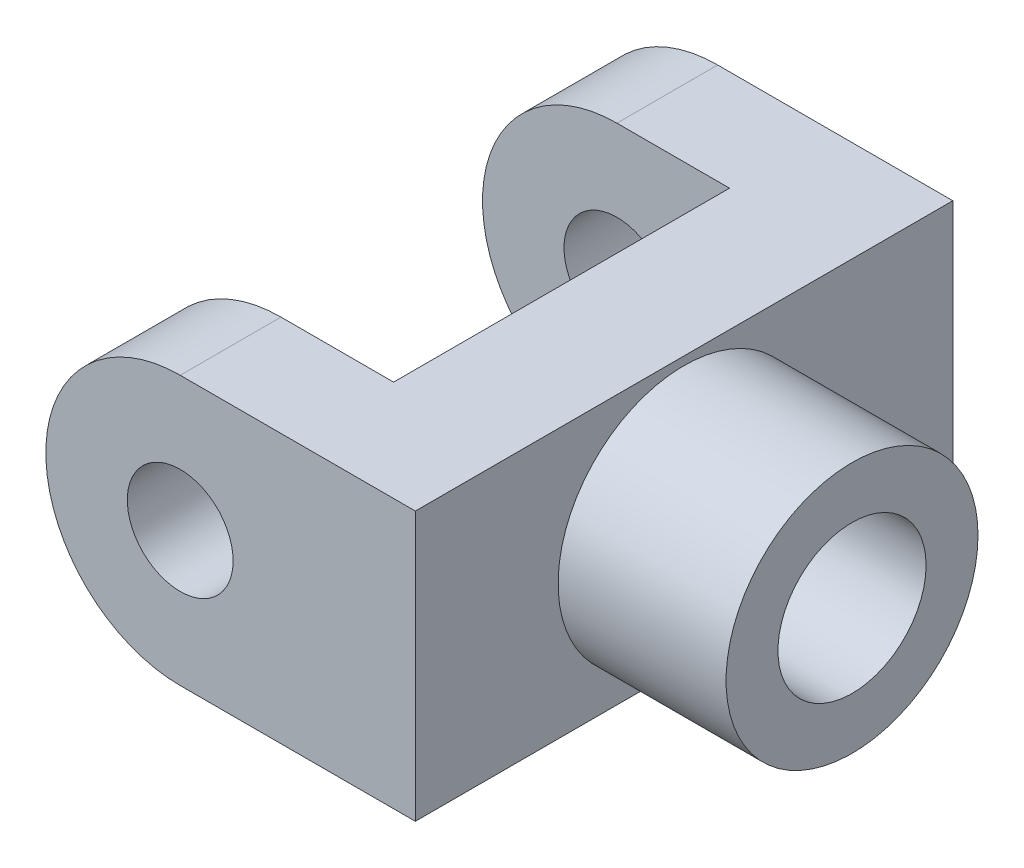
SolidWorks part; units mm, degrees
ref_plane "Front Plane" through (0, 0, 0) normal (0, 0, 1) x (1, 0, 0)
ref_plane "Top Plane" through (0, 0, 0) normal (0, 1, 0) x (1, 0, 0)
ref_plane "Right Plane" through (0, 0, 0) normal (1, 0, 0) x (0, 0, -1)
sketch "Sketch2" plane through (0, 0, 0) normal (0, 0, 1) x (1, 0, 0)
  line L0 (0, 5.08) -> (3.81, 5.08)
  line L1 (3.81, 5.08) -> (3.81, -5.08)
  line L2 (3.81, -5.08) -> (0, -5.08)
  line L3 (0, 0) -> (0, 5.08) construction
  line L4 (3.81, 5.08) -> (8.89, 5.08)
  line L5 (3.81, 5.08) -> (3.81, -5.08) construction
  line L6 (3.81, -5.08) -> (8.89, -5.08)
  line L7 (8.89, 5.08) -> (8.89, -5.08)
  circle A0 centre (0, 0) radius 2
  circle A1 centre (0, 0) radius 5.08
  dimension "D1" = 4
  dimension "D2" = 10.16
  dimension "D3" = 3.81
  dimension "D4" = 5.08
extrude "Boss-Extrude1" add sketch "Sketch2" along normal blind 20.32
ref_plane "Plane1" through (0, 0, 10.16) normal (0, 0, 1) x (1, 0, 0)
sketch "Sketch3" plane through (0, 0, 10.16) normal (0, 0, 1) x (1, 0, 0)
  line L20 (3.81, -5.08) -> (0, -5.08) construction
  line L23 (3.81, 5.08) -> (3.81, -5.08) construction
  line L28 (3.81, 5.08) -> (8.89, 5.08) construction
  line L29 (8.89, 5.08) -> (8.89, -5.08) construction
  line L30 (3.81, -5.08) -> (8.89, -5.08) construction
  line L31 (0, 5.08) -> (3.81, 5.08) construction
  line L32 (3.81, -5.08) -> (0, -5.08)
  line L33 (3.81, 5.08) -> (3.81, -5.08)
  line L34 (3.81, 5.08) -> (8.89, 5.08)
  line L35 (8.89, 5.08) -> (8.89, -5.08)
  line L36 (3.81, -5.08) -> (8.89, -5.08)
  line L37 (0, 5.08) -> (3.81, 5.08)
  circle A1 centre (0, 0) radius 5.08
  circle A5 centre (0, 0) radius 5.08
  circle A7 centre (0, 0) radius 2
  circle A8 centre (0, 0) radius 2
  dimension "D1" = 0
  dimension "D2" = 0
extrude "Cut-Extrude1" cut sketch "Sketch3" against normal mid plane 12.7 contours L33 A5 A8 | A5 L33 L37 | A5 L32 L33
sketch "Sketch4" plane through (8.89, 0, 0) normal (1, 0, 0) x (0, 0, -1)
  line L0 (-20.32, 5.08) -> (0, 5.08) construction
  circle A0 centre (-10.16, 0) radius 4.7625
  point P2 (-10.16, 5.08)
  point P3 (0, 0)
  dimension "D1" = 9.525
extrude "Boss-Extrude2" add sketch "Sketch4" along normal blind 6.35
sketch "Sketch5" plane through (15.24, 0, 0) normal (1, 0, 0) x (0, 0, -1)
  circle A0 centre (-10.16, 0) radius 4.7625 construction
  circle A1 centre (-10.16, 0) radius 4.7625 construction
  circle A2 centre (-10.16, 0) radius 2.8
  dimension "D1" = 5.6
extrude "Cut-Extrude2" cut sketch "Sketch5" against normal blind 4.7
chamfer "Chamfer2" distance 2.54 angle 10 2 edges at (3.81, -5.08, 10.16) (3.81, 5.08, 10.16)
